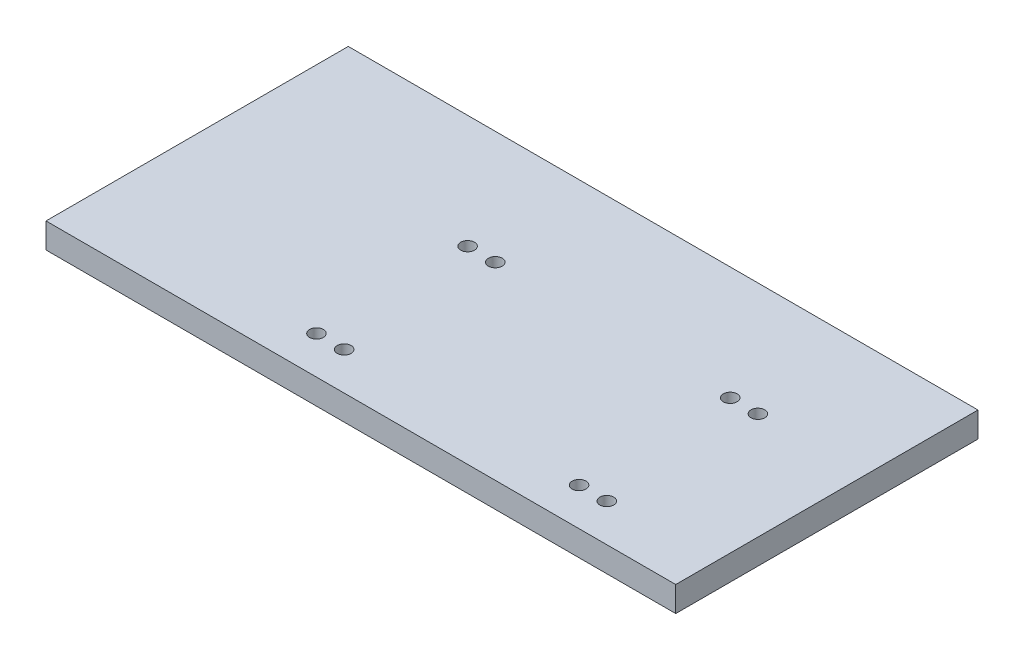
SolidWorks part; units mm, degrees
ref_plane "Front Plane" through (0, 0, 0) normal (0, 0, 1) x (1, 0, 0)
ref_plane "Top Plane" through (0, 0, 0) normal (0, 1, 0) x (1, 0, 0)
ref_plane "Right Plane" through (0, 0, 0) normal (1, 0, 0) x (0, 0, -1)
sketch "Sketch1" plane through (0, 0, 0) normal (0, 1, 0) x (1, 0, 0)
  line L1 (0, 0) -> (250, 0)
  line L2 (0, 0) -> (0, 120)
  line L3 (0, 120) -> (250, 120)
  line L4 (250, 0) -> (250, 120)
  dimension "D1" = 120
  dimension "D2" = 250
extrude "Boss-Extrude1" add sketch "Sketch1" along normal blind 10
sketch "Sketch2" plane through (0, 10, 0) normal (0, 1, 0) x (1, 0, 0)
  line L0 (0, 0) -> (250, 0) construction
  point P0 (207.6256, 15)
  point P1 (207.6256, 75)
  point P2 (196.6256, 75)
  point P3 (196.6256, 15)
  dimension "D1" = 60
  dimension "D2" = 11
  dimension "D3" = 11
  dimension "D4" = 15
hole_wizard "M5 Clearance Hole1" positions "Sketch3" profile "Sketch4" hole size "M5" standard "BSI" end condition through all
sketch "Sketch3" plane through (0, 10, 0) normal (0, 1, 0) x (1, 0, 0)
  point P0 (196.6256, 15)
  point P3 (207.6256, 15)
  point P6 (207.6256, 75)
  point P9 (196.6256, 75)
sketch "Sketch4" plane through (196.6256, 10, -15) normal (1, 0, 0) x (0, 0, 1)
  line L0 (0, 0) -> (0, 10)
  line L1 (0, 10) -> (2.75, 10)
  line L2 (2.75, 10) -> (2.75, 0)
  line L5 (2.75, 0) -> (0, 0)
  line L11 (0, -6.35) -> (0, 107.95) construction
  dimension "Thru Hole Dia." = 5.5
  dimension "Thru Hole Depth" = 10
sketch "Sketch5" plane through (0, 0, 0) normal (0, -1, 0) x (-1, 0, 0)
  line L0 (-196.6256, 15) -> (-207.6256, 15) construction
  line L1 (-196.6256, 8.75) -> (-207.6256, 8.75)
  line L2 (-196.6256, 21.25) -> (-207.6256, 21.25)
  line L3 (-196.6256, 75) -> (-207.6256, 75) construction
  line L4 (-196.6256, 68.75) -> (-207.6256, 68.75)
  line L5 (-196.6256, 81.25) -> (-207.6256, 81.25)
  arc A0 (-196.6256, 8.75) -> (-196.6256, 21.25) centre (-196.6256, 15) ccw
  arc A1 (-207.6256, 21.25) -> (-207.6256, 8.75) centre (-207.6256, 15) ccw
  arc A2 (-196.6256, 68.75) -> (-196.6256, 81.25) centre (-196.6256, 75) ccw
  arc A3 (-207.6256, 81.25) -> (-207.6256, 68.75) centre (-207.6256, 75) ccw
  point P4 (-202.1256, 15)
  point P13 (-202.1256, 75)
  dimension "D2" = 12.5
  dimension "D1" = 12.5
extrude "Cut-Extrude1" cut sketch "Sketch5" against normal blind 5
sketch "Sketch6" plane through (0, 0, 0) normal (0, -1, 0) x (1, 0, 0)
  line L0 (150, 0) -> (150, -120) construction
  line L1 (0, 0) -> (250, 0) construction
  line L2 (250, -120) -> (0, -120) construction
  line L3 (250, 0) -> (250, -120) construction
  dimension "D1" = 100
ref_plane "Plane1" through (150, 0, 0) normal (1, 0, 0) x (0, 0, -1)
mirror "Mirror1" about plane through (150, 0, 0) normal (1, 0, 0) of "M5 Clearance Hole1", "Cut-Extrude1"
